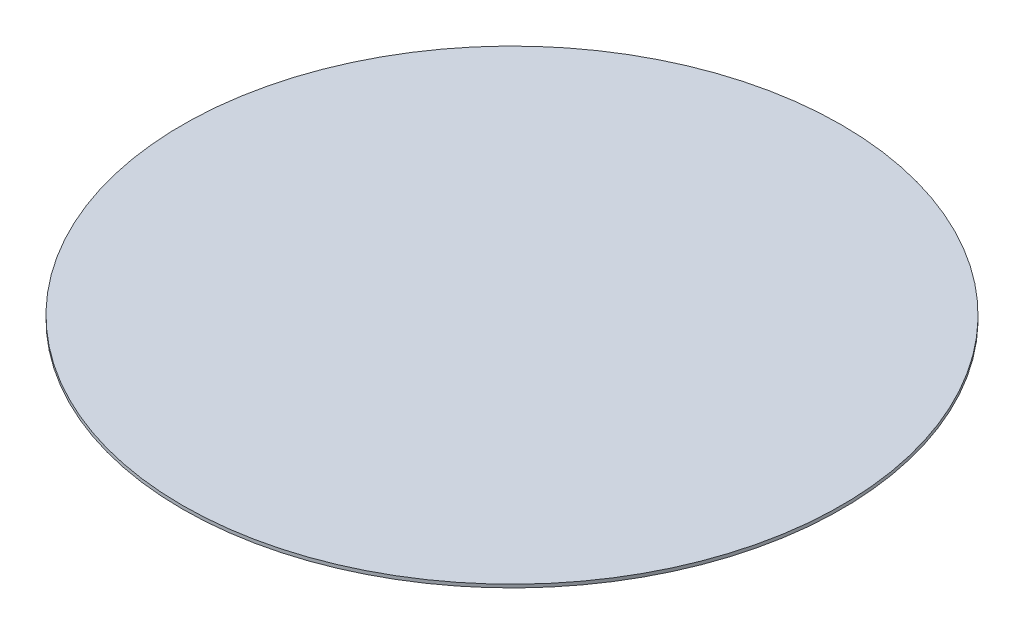
SolidWorks part; units mm, degrees
ref_plane "Front Plane" through (0, 0, 0) normal (0, 0, 1) x (1, 0, 0)
ref_plane "Top Plane" through (0, 0, 0) normal (0, 1, 0) x (1, 0, 0)
ref_plane "Right Plane" through (0, 0, 0) normal (1, 0, 0) x (0, 0, -1)
sketch "Sketch1" plane through (0, 0, 0) normal (0, 1, 0) x (1, 0, 0)
  circle A0 centre (0, 0) radius 25.8128
  dimension "D1" = 51.6255
extrude "Boss-Extrude1" add sketch "Sketch1" along normal blind 0.254
